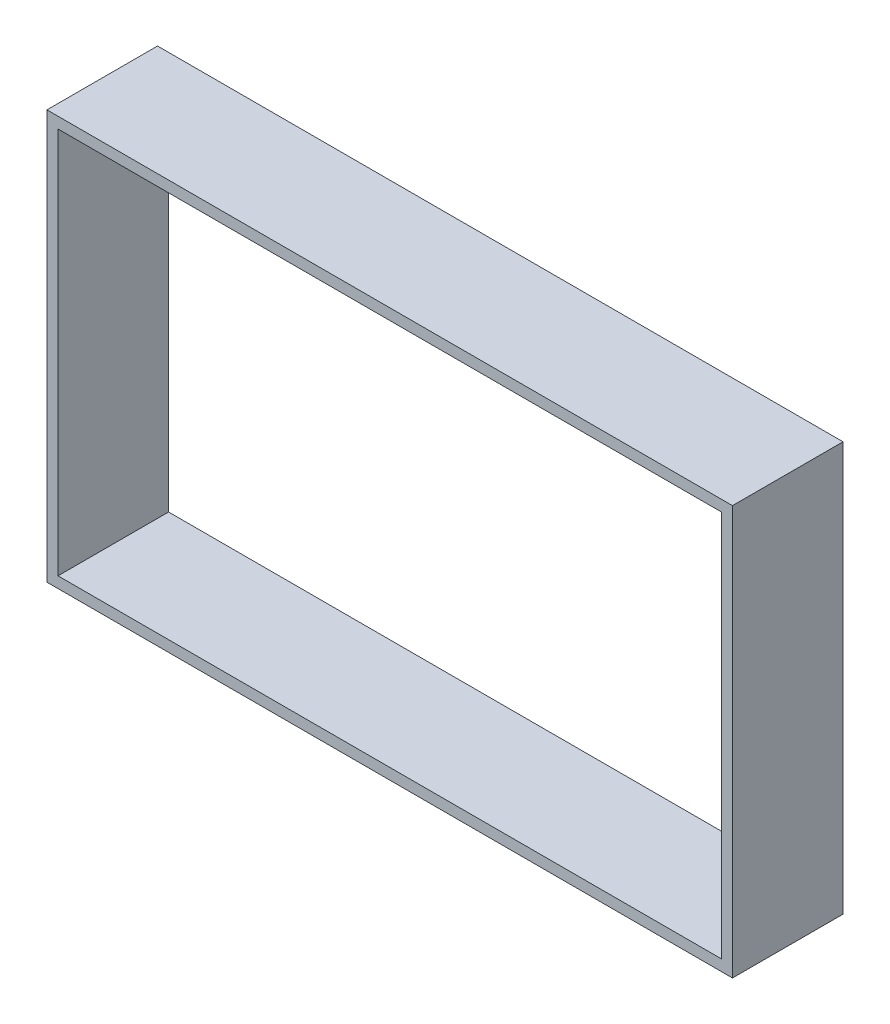
SolidWorks part; units mm, degrees
ref_plane "Front Plane" through (0, 0, 0) normal (0, 0, 1) x (1, 0, 0)
ref_plane "Top Plane" through (0, 0, 0) normal (0, 1, 0) x (1, 0, 0)
ref_plane "Right Plane" through (0, 0, 0) normal (1, 0, 0) x (0, 0, -1)
sketch "Sketch1" plane through (0, 0, 0) normal (0, 0, 1) x (1, 0, 0)
  line L1 (-30, -17.5) -> (30, -17.5)
  line L2 (-30, -17.5) -> (-30, 17.5)
  line L3 (-30, 17.5) -> (30, 17.5)
  line L4 (30, -17.5) -> (30, 17.5)
  line L5 (-30, -17.5) -> (30, 17.5) construction
  line L6 (-30, 17.5) -> (30, -17.5) construction
  point P0 (0, 0)
  dimension "D1" = 35
  dimension "D2" = 60
extrude "Extrude-Thin1" add sketch "Sketch1" along normal blind 10 thin
